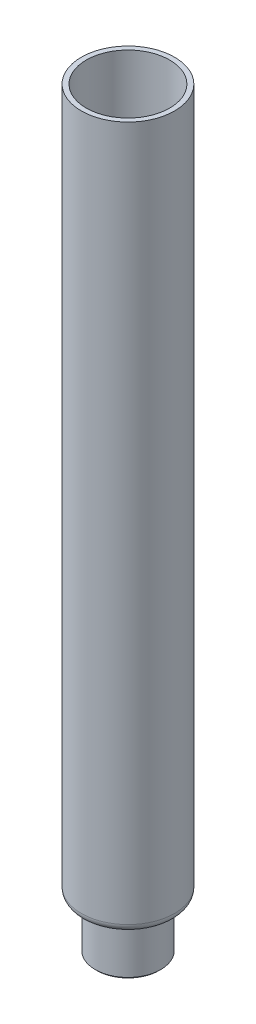
SolidWorks part; units mm, degrees
ref_plane "Plan de face" through (0, 0, 0) normal (0, 0, 1) x (1, 0, 0)
ref_plane "Plan de dessus" through (0, 0, 0) normal (0, 1, 0) x (1, 0, 0)
ref_plane "Plan de droite" through (0, 0, 0) normal (1, 0, 0) x (0, 0, -1)
sketch "Esquisse1" plane through (0, 0, 0) normal (0, 0, 1) x (1, 0, 0)
  line L0 (0, 34.9013) -> (0, -16.3052) construction
  line L1 (8.5, -15) -> (8.5, -1)
  line L2 (11, 1.5) -> (11.75, 1.5)
  line L3 (12.75, 2.5) -> (12.75, 215)
  line L4 (10, -15) -> (10, -1)
  line L5 (11, 0) -> (11.75, 0)
  line L6 (14.25, 2.5) -> (14.25, 215)
  line L7 (12.75, 215) -> (14.25, 215)
  line L8 (8.5, -15) -> (10, -15)
  line L9 (8.5, 1.5) -> (12.75, 1.5) construction
  line L10 (12.75, 1.5) -> (12.75, 215) construction
  line L11 (10, -15) -> (10, 0) construction
  line L12 (10, 0) -> (14.25, 0) construction
  line L13 (8.5, -15) -> (8.5, 1.5) construction
  line L14 (14.25, 0) -> (14.25, 215) construction
  arc A0 (11.75, 1.5) -> (12.75, 2.5) centre (11.75, 2.5) ccw
  arc A1 (10, -1) -> (11, 0) centre (11, -1) cw
  arc A2 (8.5, -1) -> (11, 1.5) centre (11, -1) cw
  arc A3 (14.25, 2.5) -> (11.75, 0) centre (11.75, 2.5) cw
  dimension "D4" = 1
  dimension "D5" = 2.5
  dimension "D2" = 28.5
  dimension "D3" = 20
  dimension "D6" = 215
  dimension "D7" = 15
  dimension "D1" = 1.5
revolve "Révolution1" add sketch "Esquisse1" angle 360 about L0
chamfer "Chanfrein1" distance 0.5 angle 45 1 edges at (0, -15, 10)
